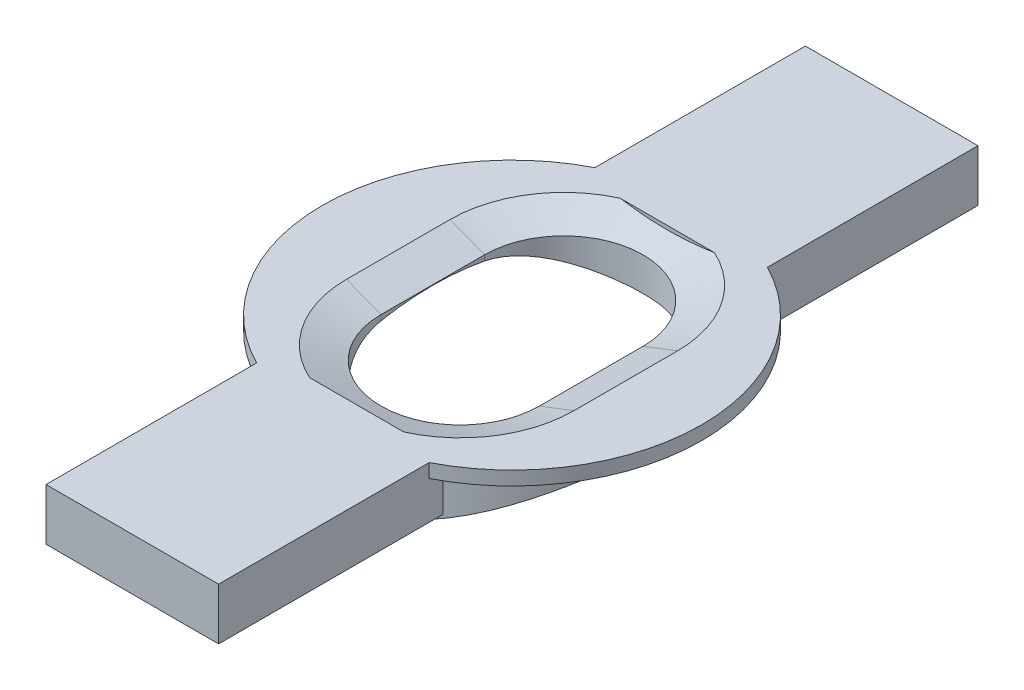
SolidWorks part; units mm, degrees
ref_plane "Front Plane" through (0, 0, 0) normal (0, 0, 1) x (1, 0, 0)
ref_plane "Top Plane" through (0, 0, 0) normal (0, 1, 0) x (1, 0, 0)
ref_plane "Right Plane" through (0, 0, 0) normal (1, 0, 0) x (0, 0, -1)
sketch "Sketch1" plane through (0, 0, 0) normal (0, 1, 0) x (1, 0, 0)
  circle A0 centre (0, 0) radius 5
extrude "Boss-Extrude1" add sketch "Sketch1" along normal blind 5
sketch "Sketch2" plane through (0, 5, 0) normal (0, 1, 0) x (1, 0, 0)
  circle A0 centre (0, 0) radius 5.5
extrude "Boss-Extrude2" add sketch "Sketch2" along normal blind 0.4
sketch "Sketch4" plane through (0, 5.4, 0) normal (0, 1, 0) x (1, 0, 0)
  line L0 (0, 1.5) -> (0, -1.5) construction
  line L1 (2.2953, 1.5) -> (2.2953, -1.5)
  line L2 (-2.2953, 1.5) -> (-2.2953, -1.5)
  arc A0 (2.2953, 1.5) -> (-2.2953, 1.5) centre (0, 1.5) ccw
  arc A1 (-2.2953, -1.5) -> (2.2953, -1.5) centre (0, -1.5) ccw
  point P3 (0, 0)
  dimension "D1" = 1.5
  dimension "D2" = 1.5
extrude "Cut-Extrude1" cut sketch "Sketch4" against normal through all
sketch "Sketch5" plane through (0, 0, 0) normal (1, 0, 0) x (0, 0, -1)
  circle A0 centre (0, -3) radius 8
extrude "Cut-Extrude2" cut sketch "Sketch5" against normal through all and the other way through all
sketch "Sketch6" plane through (0, 5.4, 0) normal (0, 1, 0) x (-1, 0, 0)
  circle A0 centre (0, 0) radius 5
chamfer "Chamfer4" distance 1 angle 21 4 edges at (0, 5.4, -3.7953) (-2.2953, 5.4, 0) (2.2953, 5.4, 0) (0, 5.4, 3.7953)
sketch "Sketch7" plane through (0, 5.4, 0) normal (0, 1, 0) x (1, 0, 0)
  line L1 (-2.5, 4.5) -> (2.5, 4.5)
  line L2 (-2.5, 4.5) -> (-2.5, 11)
  line L3 (-2.5, 11) -> (2.5, 11)
  line L4 (2.5, 4.5) -> (2.5, 11)
  line L5 (-2.5, -4.5) -> (2.5, -4.5)
  line L6 (-2.5, -4.5) -> (-2.5, -11)
  line L7 (-2.5, -11) -> (2.5, -11)
  line L8 (2.5, -4.5) -> (2.5, -11)
extrude "Boss-Extrude4" add sketch "Sketch7" against normal blind 1.5
